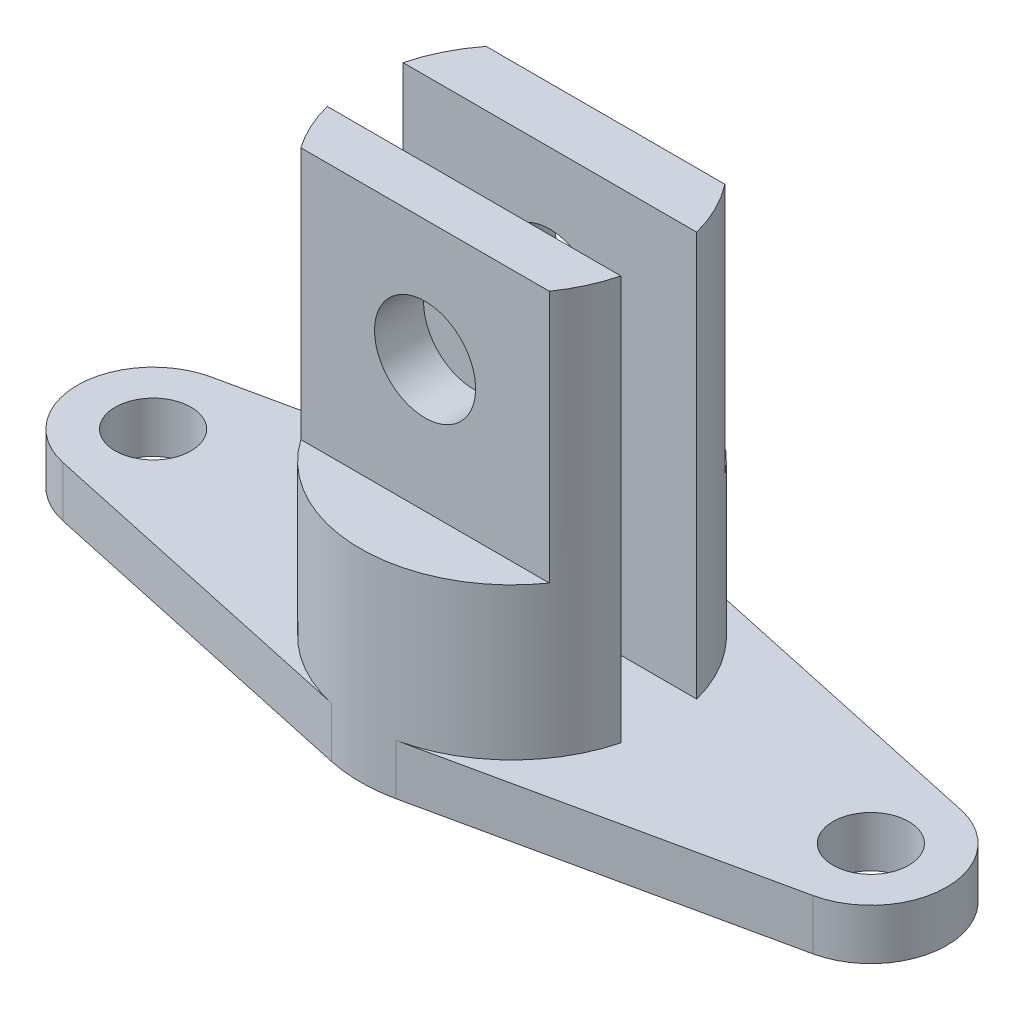
SolidWorks part; units mm, degrees
ref_plane "Alzado" through (0, 0, 0) normal (0, 0, 1) x (1, 0, 0)
ref_plane "Planta" through (0, 0, 0) normal (0, 1, 0) x (1, 0, 0)
ref_plane "Vista lateral" through (0, 0, 0) normal (1, 0, 0) x (0, 0, -1)
sketch "Croquis1" plane through (0, 0, 0) normal (0, 1, 0) x (1, 0, 0)
  line L0 (-71, 0) -> (0, 0) construction
  line L1 (-74.169, 14.6614) -> (-6.338, 29.3228)
  line L2 (-74.169, -14.6614) -> (-6.338, -29.3228)
  line L3 (0, 152.3424) -> (0, -152.3424) construction
  line L4 (74.169, -14.6614) -> (6.338, -29.3228)
  line L5 (74.169, 14.6614) -> (6.338, 29.3228)
  line L6 (63.5, 0) -> (71, 0) construction
  line L7 (0, 7.5) -> (0, -7.5) construction
  line L8 (-29.0474, 7.5) -> (29.0474, 7.5)
  line L9 (-29.0474, -7.5) -> (29.0474, -7.5)
  line L10 (0, 18.5) -> (0, -18.5)
  line L11 (-23.6167, 18.5) -> (23.6167, 18.5)
  line L12 (-23.6167, -18.5) -> (23.6167, -18.5)
  circle A4 centre (0, 0) radius 30
  circle A5 centre (-71, 0) radius 7.5
  circle A6 centre (71, 0) radius 7.5
  arc A7 (-74.169, 14.6614) -> (-74.169, -14.6614) centre (-71, 0) ccw
  arc A8 (74.169, -14.6614) -> (74.169, 14.6614) centre (71, 0) ccw
  point P6 (0, 0)
  point P19 (0, 0)
  point P23 (0, 0)
  point P26 (0, 7.5)
  point P29 (0, -7.5)
  point P32 (0, 0)
  point P35 (0, 18.5)
  point P37 (0, -18.5)
  dimension "D2" = 60
  dimension "D3" = 15
  dimension "D4" = 15
  dimension "D5" = 30
  dimension "D6" = 30
  dimension "D7" = 15
  dimension "D1" = 142
  dimension "D8" = 7.5
  dimension "D9" = 37
extrude "Saliente-Extruir1" add sketch "Croquis1" along normal blind 10 contours A4 L12 | L12 A4 L9 L10 | L9 A4 L8 L10 | L9 A4 L12 L10 | L8 A4 L9 L10 | L11 A4 L8 L10 | L8 A4 L11 L10 | L11 A4 | L4 A8 L5 A4 A6 | L1 A7 L2 A4 A5
sketch "Croquis2" plane through (0, 10, 0) normal (0, 1, 0) x (1, 0, 0)
  line L0 (0, 7.5) -> (0, -7.5) construction
  line L1 (-30, 0) -> (30, 0) construction
  line L2 (-29.0474, 7.5) -> (29.0474, 7.5)
  line L3 (-29.0474, -7.5) -> (29.0474, -7.5)
  circle A0 centre (0, 0) radius 30
  point P6 (0, 0)
  point P9 (0, 0)
  point P10 (0, 0)
  point P13 (0, 7.5)
  point P15 (0, -7.5)
  arc M2 (6.338, 29.3228) -> (-6.338, 29.3228) centre (0, 0) ccw
  arc M6 (-6.338, -29.3228) -> (6.338, -29.3228) centre (0, 0) ccw
  dimension "D2" = 60
  dimension "D1" = 15
  dimension "D3" = 7.5
extrude "Saliente-Extruir2" add sketch "Croquis2" along normal blind 80 contours A0 L3 M6 | L2 A0 M2
sketch "Croquis4" plane through (0, 90, 0) normal (0, 1, 0) x (1, 0, 0)
  line L1 (-23.6167, 18.5) -> (23.6167, 18.5)
  arc A0 (29.0474, 7.5) -> (-29.0474, 7.5) centre (0, 0) ccw construction
  arc A1 (23.6167, 18.5) -> (-23.6167, 18.5) centre (0, 0) ccw
  dimension "D1" = 18.5
extrude "Cortar-Extruir1" cut sketch "Croquis4" against normal blind 50
sketch "Croquis5" plane through (0, 0, -18.5) normal (0, 0, -1) x (-1, 0, 0)
  line L0 (23.6167, 90) -> (-23.6167, 90) construction
  line L5 (-23.6167, 40) -> (23.6167, 40) construction
  line L6 (-23.6167, 90) -> (23.6167, 90) construction
  line L7 (0, 40) -> (0, 90) construction
  circle A0 centre (0, 66) radius 10
  point P6 (0, 0)
  dimension "D1" = 20
  dimension "D2" = 24
  dimension "D3" = 47.2335
extrude "Cortar-Extruir2" cut sketch "Croquis5" against normal blind 50
sketch "Croquis6" plane through (0, 90, 0) normal (0, 1, 0) x (1, 0, 0)
  line L1 (-24.5793, -17.2005) -> (24.5793, -17.2005)
  arc A0 (-29.0474, -7.5) -> (29.0474, -7.5) centre (0, 0) ccw construction
  arc A3 (-24.5793, -17.2005) -> (24.5793, -17.2005) centre (0, 0) ccw
  point P9 (0, -17.2005)
  dimension "D1" = 49.1586
extrude "Cortar-Extruir3" cut sketch "Croquis6" against normal blind 50
